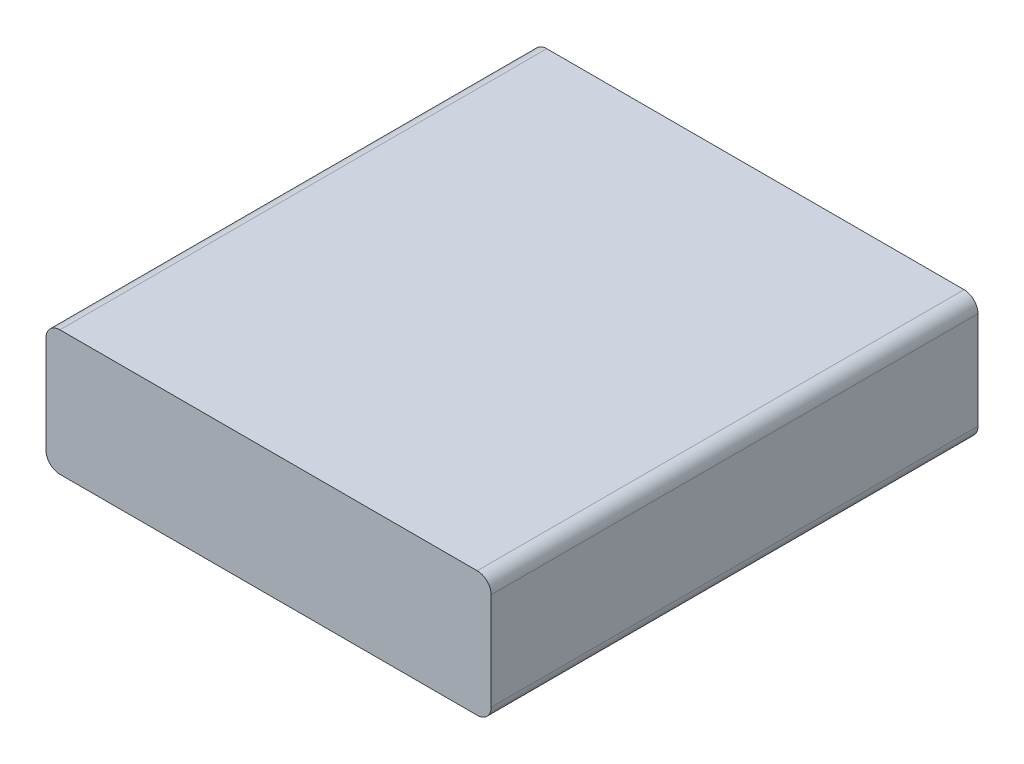
SolidWorks part; units mm, degrees
ref_plane "前基準面" through (0, 0, 0) normal (0, 0, 1) x (1, 0, 0)
ref_plane "上基準面" through (0, 0, 0) normal (0, 1, 0) x (1, 0, 0)
ref_plane "右基準面" through (0, 0, 0) normal (1, 0, 0) x (0, 0, -1)
sketch "草圖1" plane through (0, 0, 0) normal (0, 0, 1) x (1, 0, 0)
  line L1 (0, 0) -> (64, 0)
  line L2 (0, 0) -> (0, 18)
  line L3 (0, 18) -> (64, 18)
  line L4 (64, 0) -> (64, 18)
  dimension "D1" = 64
  dimension "D2" = 18
extrude "填料-伸長1" add sketch "草圖1" along normal blind 70
fillet "圓角1" radius 2 4 edges at (64, 0, 35) (0, 0, 35) (0, 18, 35) (64, 18, 35)
sketch "草圖2" plane through (0, 18, 0) normal (0, 1, 0) x (1, 0, 0)
  line L1 (9.0615, -64.4212) -> (51.4997, -64.4212)
  line L2 (9.0615, -64.4212) -> (9.0615, -44.9113)
  line L3 (9.0615, -44.9113) -> (51.4997, -44.9113)
  line L4 (51.4997, -64.4212) -> (51.4997, -44.9113)
  line L5 (10.8302, -26.9553) -> (51.4997, -26.9553)
  line L6 (10.8302, -26.9553) -> (10.8302, -6.4851)
  line L7 (10.8302, -6.4851) -> (51.4997, -6.4851)
  line L8 (51.4997, -26.9553) -> (51.4997, -6.4851)
extrude "填料-伸長2" [suppressed] add sketch "草圖2" along normal blind 2 separate body
